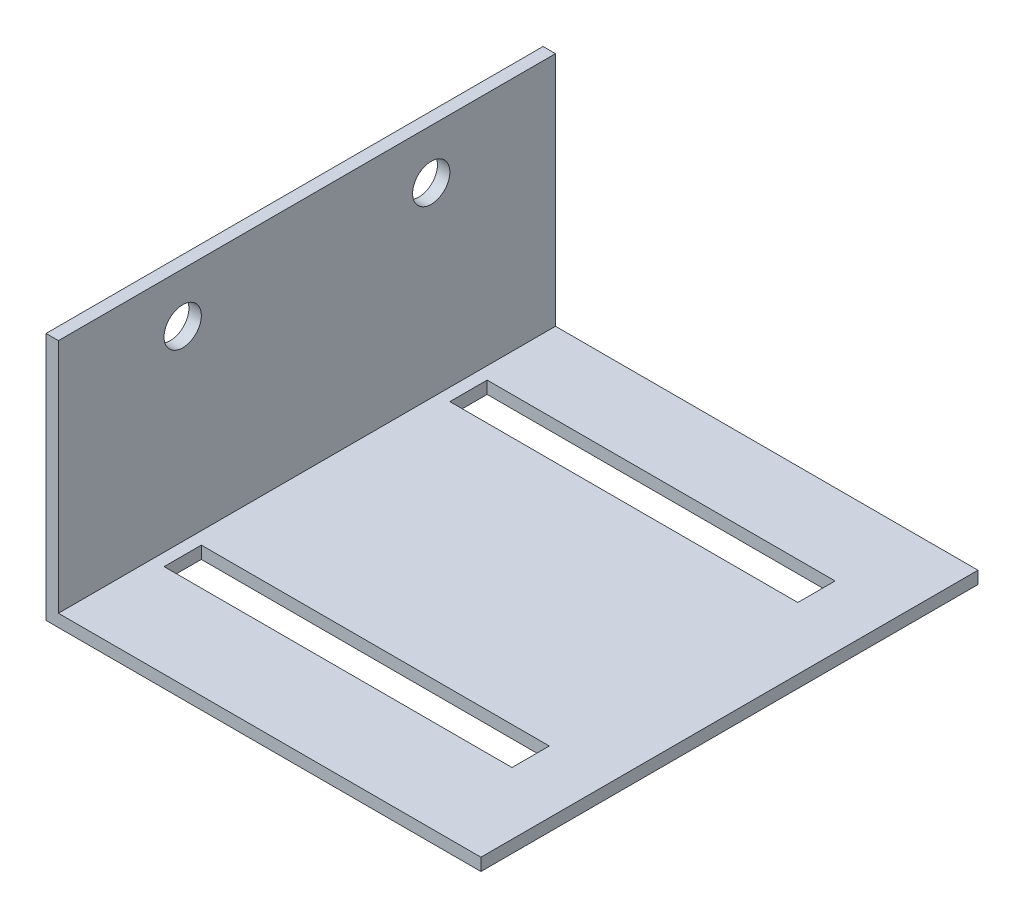
SolidWorks part; units mm, degrees
ref_plane "Front Plane" through (0, 0, 0) normal (0, 0, 1) x (1, 0, 0)
ref_plane "Top Plane" through (0, 0, 0) normal (0, 1, 0) x (1, 0, 0)
ref_plane "Right Plane" through (0, 0, 0) normal (1, 0, 0) x (0, 0, -1)
sketch "Sketch1" plane through (0, 0, 0) normal (0, 0, 1) x (1, 0, 0)
  line L0 (0, 0) -> (35, 0)
  line L1 (35, 0) -> (35, 1)
  line L2 (35, 1) -> (1, 1)
  line L3 (1, 1) -> (1, 20)
  line L4 (1, 20) -> (0, 20)
  line L5 (0, 20) -> (0, 0)
  dimension "D1" = 34
  dimension "D2" = 1
  dimension "D3" = 19
  dimension "D4" = 1
  dimension "D5" = 20
  dimension "D6" = 35
extrude "Boss-Extrude1" add sketch "Sketch1" along normal blind 40
sketch "Sketch2" plane through (0, 1, 0) normal (0, 1, 0) x (1, 0, 0)
  line L0 (35, -40) -> (35, 0) construction
  line L1 (2, -6.5) -> (30, -6.5)
  line L2 (2, -6.5) -> (2, -9.5)
  line L3 (2, -9.5) -> (30, -9.5)
  line L4 (30, -6.5) -> (30, -9.5)
  line L5 (35, 0) -> (1, 0) construction
  line L6 (2, -32.5) -> (30, -32.5)
  line L7 (2, -32.5) -> (2, -29.5)
  line L8 (2, -29.5) -> (30, -29.5)
  line L9 (30, -32.5) -> (30, -29.5)
  point P10 (2, -8)
  point P11 (2, -31)
  dimension "D1" = 3
  dimension "D2" = 28
  dimension "D3" = 5
  dimension "D4" = 3
  dimension "D5" = 28
  dimension "D6" = 23
  dimension "D7" = 5
  dimension "D8" = 8
extrude "Cut-Extrude1" cut sketch "Sketch2" against normal blind 10
sketch "Sketch3" plane through (0, 0, 0) normal (-1, 0, 0) x (0, 0, 1)
  line L0 (0, 20) -> (0, 0) construction
  line L1 (40, 20) -> (40, 0) construction
  line L2 (40, 0) -> (0, 0) construction
  circle A0 centre (30, 16) radius 1.5
  circle A1 centre (10, 16) radius 1.5
  dimension "D1" = 3
  dimension "D2" = 3
  dimension "D4" = 10
  dimension "D5" = 16
  dimension "D6" = 3
  dimension "D7" = 16
  dimension "D3" = 10
extrude "Cut-Extrude2" cut sketch "Sketch3" against normal blind 10
